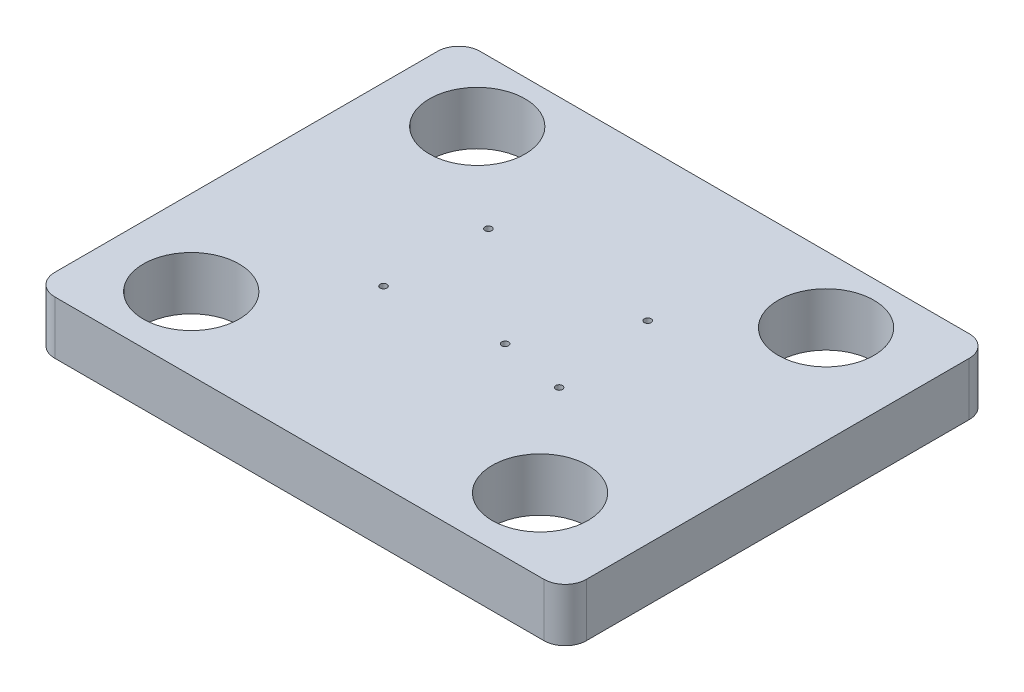
SolidWorks part; units mm, degrees
ref_plane "Front Plane" through (0, 0, 0) normal (0, 0, 1) x (1, 0, 0)
ref_plane "Top Plane" through (0, 0, 0) normal (0, 1, 0) x (1, 0, 0)
ref_plane "Right Plane" through (0, 0, 0) normal (1, 0, 0) x (0, 0, -1)
sketch "Sketch2" plane through (0, 0, 0) normal (0, 1, 0) x (1, 0, 0)
  line L1 (0, 0) -> (250, 0)
  line L2 (0, 0) -> (0, 200)
  line L3 (0, 200) -> (250, 200)
  line L4 (250, 0) -> (250, 200)
  dimension "D1" = 250
  dimension "D2" = 200
extrude "Boss-Extrude1" add sketch "Sketch2" along normal blind 25
fillet "Fillet1" radius 10 1 edges at (0, 12.5, 0)
fillet "Fillet2" radius 10 1 edges at (250, 12.5, 0)
fillet "Fillet3" radius 10 1 edges at (250, 12.5, -200)
fillet "Fillet4" radius 10 1 edges at (0, 12.5, -200)
sketch "Sketch3" plane through (0, 25, 0) normal (0, 1, 0) x (1, 0, 0)
  line L1 (68.9439, 132.4761) -> (170.5439, 132.4761)
  line L2 (68.9439, 132.4761) -> (68.9439, 79.1361)
  line L3 (68.9439, 79.1361) -> (170.5439, 79.1361)
  line L4 (170.5439, 132.4761) -> (170.5439, 79.1361)
  circle A0 centre (84.1839, 129.7121) radius 1.6
  circle A1 centre (82.9139, 81.6761) radius 1.6
  circle A2 centre (165.4639, 81.6761) radius 1.6
  circle A3 centre (159.1139, 129.7121) radius 1.6
  circle A4 centre (134.9839, 86.7561) radius 1.6
  dimension "D3" = 3.2
  dimension "D1" = 101.6
  dimension "D2" = 53.34
  dimension "D4" = 15.24
  dimension "D5" = 13.97
  dimension "D6" = 2.54
  dimension "D7" = 96.52
  dimension "D8" = 90.17
  dimension "D9" = 7.62
  dimension "D10" = 66.04
extrude "Cut-Extrude1" cut sketch "Sketch3" against normal through all contours A1 | A0 | A3 | A2 | A4
sketch "Sketch4" plane through (0, 25, 0) normal (0, 1, 0) x (1, 0, 0)
  circle A0 centre (203.931, 168.7504) radius 22.5
  circle A1 centre (203.931, 34.2661) radius 22.5
  circle A2 centre (39.9104, 34.2661) radius 22.5
  circle A3 centre (39.9104, 168.7504) radius 22.5
  dimension "D1" = 45
extrude "Cut-Extrude2" cut sketch "Sketch4" against normal through all
